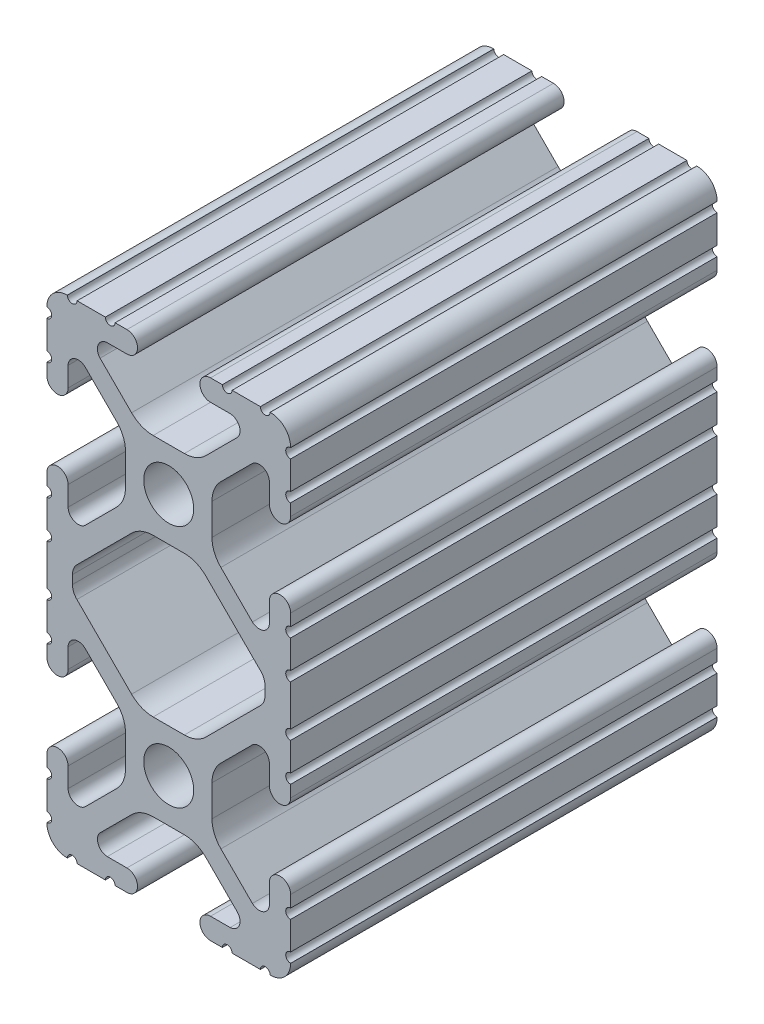
SolidWorks part; units mm, degrees
ref_plane "Front Plane" through (0, 0, 0) normal (0, 0, 1) x (1, 0, 0)
ref_plane "Top Plane" through (0, 0, 0) normal (0, 1, 0) x (1, 0, 0)
ref_plane "Right Plane" through (0, 0, 0) normal (1, 0, 0) x (0, 0, -1)
sketch "Sketch1" plane through (0, 0, 0) normal (0, 0, 1) x (1, 0, 0)
  line L0 (902.297, 599.2494) -> (902.297, 600.1524)
  line L1 (902.7583, 601.2659) -> (908.4588, 606.9666)
  line L2 (910.7039, 607.8966) -> (913.9563, 607.8966)
  line L3 (916.2014, 606.9666) -> (921.9018, 601.266)
  line L4 (922.363, 600.1525) -> (922.363, 599.2495)
  line L5 (921.9018, 598.136) -> (916.2013, 592.4353)
  line L6 (913.9562, 591.5053) -> (910.7038, 591.5053)
  line L7 (908.4587, 592.4353) -> (902.7583, 598.1358)
  line L8 (925.03, 602.8505) -> (925.03, 605.7969)
  line L9 (925.03, 606.8129) -> (925.03, 608.0448)
  line L10 (922.8202, 608.0448) -> (922.8202, 605.996)
  line L11 (921.0484, 605.2457) -> (917.7644, 608.5297)
  line L12 (916.8344, 610.7748) -> (916.8344, 614.0272)
  line L13 (917.7644, 616.2723) -> (921.0482, 619.556)
  line L14 (922.8202, 618.7995) -> (922.8202, 616.757)
  line L15 (925.03, 616.757) -> (925.03, 617.9889)
  line L16 (925.03, 619.0049) -> (925.03, 621.9513)
  line L17 (925.03, 622.9673) -> (925.03, 622.9927)
  line L18 (922.9218, 625.1009) -> (922.8964, 625.1009)
  line L19 (921.8804, 625.1009) -> (918.934, 625.1009)
  line L20 (917.918, 625.1009) -> (916.6861, 625.1009)
  line L21 (916.6861, 622.8911) -> (918.735, 622.8911)
  line L22 (919.4852, 621.1193) -> (916.2013, 617.8353)
  line L23 (913.9562, 616.9053) -> (910.7038, 616.9053)
  line L24 (908.4587, 617.8353) -> (905.175, 621.1191)
  line L25 (905.9315, 622.8911) -> (907.9739, 622.8911)
  line L26 (907.9739, 625.1009) -> (906.742, 625.1009)
  line L27 (905.726, 625.1009) -> (902.7796, 625.1009)
  line L28 (901.7636, 625.1009) -> (901.7382, 625.1009)
  line L29 (899.63, 622.9927) -> (899.63, 622.9673)
  line L30 (899.63, 621.9513) -> (899.63, 619.0049)
  line L31 (899.63, 617.9889) -> (899.63, 616.757)
  line L32 (901.8398, 616.757) -> (901.8398, 618.8059)
  line L33 (903.6117, 619.5561) -> (906.8957, 616.2722)
  line L34 (907.8257, 614.0271) -> (907.8257, 610.7747)
  line L35 (906.8957, 608.5296) -> (903.6119, 605.2459)
  line L36 (901.8398, 606.0024) -> (901.8398, 608.0448)
  line L37 (899.63, 608.0448) -> (899.63, 606.8129)
  line L38 (899.63, 605.7969) -> (899.63, 602.8505)
  line L39 (899.63, 601.8345) -> (899.63, 597.5673)
  line L40 (899.63, 596.5513) -> (899.63, 593.6049)
  line L41 (899.63, 592.5889) -> (899.63, 591.357)
  line L42 (901.8398, 591.357) -> (901.8398, 593.4059)
  line L43 (903.6117, 594.1561) -> (906.8957, 590.8722)
  line L44 (907.8257, 588.6271) -> (907.8257, 585.3747)
  line L45 (906.8957, 583.1296) -> (903.6119, 579.8459)
  line L46 (901.8398, 580.6024) -> (901.8398, 582.6448)
  line L47 (899.63, 582.6448) -> (899.63, 581.4129)
  line L48 (899.63, 580.3969) -> (899.63, 577.4505)
  line L49 (899.63, 576.4345) -> (899.63, 576.4091)
  line L50 (901.7382, 574.3009) -> (901.7636, 574.3009)
  line L51 (902.7796, 574.3009) -> (905.726, 574.3009)
  line L52 (906.742, 574.3009) -> (907.9739, 574.3009)
  line L53 (907.9739, 576.5107) -> (905.9251, 576.5107)
  line L54 (905.1749, 578.2826) -> (908.4588, 581.5666)
  line L55 (910.7039, 582.4966) -> (913.9563, 582.4966)
  line L56 (916.2014, 581.5666) -> (919.4851, 578.2828)
  line L57 (918.7286, 576.5107) -> (916.6861, 576.5107)
  line L58 (916.6861, 574.3009) -> (917.918, 574.3009)
  line L59 (918.934, 574.3009) -> (921.8804, 574.3009)
  line L60 (922.8964, 574.3009) -> (922.9218, 574.3009)
  line L61 (925.03, 576.4091) -> (925.03, 576.4345)
  line L62 (925.03, 577.4505) -> (925.03, 580.3969)
  line L63 (925.03, 581.4129) -> (925.03, 582.6448)
  line L64 (922.8202, 582.6448) -> (922.8202, 580.596)
  line L65 (921.0484, 579.8457) -> (917.7644, 583.1297)
  line L66 (916.8344, 585.3748) -> (916.8344, 588.6272)
  line L67 (917.7644, 590.8723) -> (921.0482, 594.156)
  line L68 (922.8202, 593.3995) -> (922.8202, 591.357)
  line L69 (925.03, 591.357) -> (925.03, 592.5889)
  line L70 (925.03, 593.6049) -> (925.03, 596.5513)
  line L71 (925.03, 597.5673) -> (925.03, 601.8345)
  arc A0 (902.7583, 601.2659) -> (902.297, 600.1524) centre (903.8718, 600.1524) ccw
  arc A1 (910.7039, 607.8966) -> (908.4588, 606.9666) centre (910.7039, 604.7216) ccw
  arc A2 (916.2014, 606.9666) -> (913.9563, 607.8966) centre (913.9563, 604.7216) ccw
  arc A3 (922.363, 600.1525) -> (921.9018, 601.266) centre (920.7882, 600.1525) ccw
  arc A4 (921.9018, 598.136) -> (922.363, 599.2495) centre (920.7882, 599.2495) ccw
  arc A5 (913.9562, 591.5053) -> (916.2013, 592.4353) centre (913.9562, 594.6803) ccw
  arc A6 (908.4587, 592.4353) -> (910.7038, 591.5053) centre (910.7038, 594.6803) ccw
  arc A7 (902.297, 599.2494) -> (902.7583, 598.1358) centre (903.8718, 599.2494) ccw
  circle A8 centre (912.33, 612.4009) radius 2.6035
  circle A9 centre (912.33, 587.0009) radius 2.6035
  arc A10 (925.03, 602.8505) -> (925.03, 601.8345) centre (925.03, 602.3425) ccw
  arc A11 (925.03, 606.8129) -> (925.03, 605.7969) centre (925.03, 606.3049) ccw
  arc A12 (925.03, 608.0448) -> (922.8202, 608.0448) centre (923.9251, 608.0448) ccw
  arc A13 (921.0484, 605.2457) -> (922.8202, 605.996) centre (921.7603, 606.0319) ccw
  arc A14 (916.8344, 610.7748) -> (917.7644, 608.5297) centre (920.0094, 610.7748) ccw
  arc A15 (917.7644, 616.2723) -> (916.8344, 614.0272) centre (920.0094, 614.0272) ccw
  arc A16 (922.8202, 618.7995) -> (921.0482, 619.556) centre (921.7601, 618.7699) ccw
  arc A17 (922.8202, 616.757) -> (925.03, 616.757) centre (923.9251, 616.757) ccw
  arc A18 (925.03, 619.0049) -> (925.03, 617.9889) centre (925.03, 618.4969) ccw
  arc A19 (925.03, 622.9673) -> (925.03, 621.9513) centre (925.03, 622.4593) ccw
  arc A20 (925.03, 622.9927) -> (922.9218, 625.1009) centre (922.9218, 622.9927) ccw
  arc A21 (921.8804, 625.1009) -> (922.8964, 625.1009) centre (922.3884, 625.1009) ccw
  arc A22 (917.918, 625.1009) -> (918.934, 625.1009) centre (918.426, 625.1009) ccw
  arc A23 (916.6861, 625.1009) -> (916.6861, 622.8911) centre (916.6861, 623.996) ccw
  arc A24 (919.4852, 621.1193) -> (918.735, 622.8911) centre (918.6991, 621.8312) ccw
  arc A25 (913.9562, 616.9053) -> (916.2013, 617.8353) centre (913.9562, 620.0803) ccw
  arc A26 (908.4587, 617.8353) -> (910.7038, 616.9053) centre (910.7038, 620.0803) ccw
  arc A27 (905.9315, 622.8911) -> (905.175, 621.1191) centre (905.9611, 621.831) ccw
  arc A28 (907.9739, 622.8911) -> (907.9739, 625.1009) centre (907.9739, 623.996) ccw
  arc A29 (905.726, 625.1009) -> (906.742, 625.1009) centre (906.234, 625.1009) ccw
  arc A30 (901.7636, 625.1009) -> (902.7796, 625.1009) centre (902.2716, 625.1009) ccw
  arc A31 (901.7382, 625.1009) -> (899.63, 622.9927) centre (901.7382, 622.9927) ccw
  arc A32 (899.63, 621.9513) -> (899.63, 622.9673) centre (899.63, 622.4593) ccw
  arc A33 (899.63, 617.9889) -> (899.63, 619.0049) centre (899.63, 618.4969) ccw
  arc A34 (899.63, 616.757) -> (901.8398, 616.757) centre (900.7349, 616.757) ccw
  arc A35 (903.6117, 619.5561) -> (901.8398, 618.8059) centre (902.8998, 618.77) ccw
  arc A36 (907.8257, 614.0271) -> (906.8957, 616.2722) centre (904.6507, 614.0271) ccw
  arc A37 (906.8957, 608.5296) -> (907.8257, 610.7747) centre (904.6507, 610.7747) ccw
  arc A38 (901.8398, 606.0024) -> (903.6119, 605.2459) centre (902.9, 606.032) ccw
  arc A39 (901.8398, 608.0448) -> (899.63, 608.0448) centre (900.7349, 608.0448) ccw
  arc A40 (899.63, 605.7969) -> (899.63, 606.8129) centre (899.63, 606.3049) ccw
  arc A41 (899.63, 601.8345) -> (899.63, 602.8505) centre (899.63, 602.3425) ccw
  arc A42 (899.63, 596.5513) -> (899.63, 597.5673) centre (899.63, 597.0593) ccw
  arc A43 (899.63, 592.5889) -> (899.63, 593.6049) centre (899.63, 593.0969) ccw
  arc A44 (899.63, 591.357) -> (901.8398, 591.357) centre (900.7349, 591.357) ccw
  arc A45 (903.6117, 594.1561) -> (901.8398, 593.4059) centre (902.8998, 593.37) ccw
  arc A46 (907.8257, 588.6271) -> (906.8957, 590.8722) centre (904.6507, 588.6271) ccw
  arc A47 (906.8957, 583.1296) -> (907.8257, 585.3747) centre (904.6507, 585.3747) ccw
  arc A48 (901.8398, 580.6024) -> (903.6119, 579.8459) centre (902.9, 580.632) ccw
  arc A49 (901.8398, 582.6448) -> (899.63, 582.6448) centre (900.7349, 582.6448) ccw
  arc A50 (899.63, 580.3969) -> (899.63, 581.4129) centre (899.63, 580.9049) ccw
  arc A51 (899.63, 576.4345) -> (899.63, 577.4505) centre (899.63, 576.9425) ccw
  arc A52 (899.63, 576.4091) -> (901.7382, 574.3009) centre (901.7382, 576.4091) ccw
  arc A53 (902.7796, 574.3009) -> (901.7636, 574.3009) centre (902.2716, 574.3009) ccw
  arc A54 (906.742, 574.3009) -> (905.726, 574.3009) centre (906.234, 574.3009) ccw
  arc A55 (907.9739, 574.3009) -> (907.9739, 576.5107) centre (907.9739, 575.4058) ccw
  arc A56 (905.1749, 578.2826) -> (905.9251, 576.5107) centre (905.961, 577.5707) ccw
  arc A57 (910.7039, 582.4966) -> (908.4588, 581.5666) centre (910.7039, 579.3216) ccw
  arc A58 (916.2014, 581.5666) -> (913.9563, 582.4966) centre (913.9563, 579.3216) ccw
  arc A59 (918.7286, 576.5107) -> (919.4851, 578.2828) centre (918.699, 577.5709) ccw
  arc A60 (916.6861, 576.5107) -> (916.6861, 574.3009) centre (916.6861, 575.4058) ccw
  arc A61 (918.934, 574.3009) -> (917.918, 574.3009) centre (918.426, 574.3009) ccw
  arc A62 (922.8964, 574.3009) -> (921.8804, 574.3009) centre (922.3884, 574.3009) ccw
  arc A63 (922.9218, 574.3009) -> (925.03, 576.4091) centre (922.9218, 576.4091) ccw
  arc A64 (925.03, 577.4505) -> (925.03, 576.4345) centre (925.03, 576.9425) ccw
  arc A65 (925.03, 581.4129) -> (925.03, 580.3969) centre (925.03, 580.9049) ccw
  arc A66 (925.03, 582.6448) -> (922.8202, 582.6448) centre (923.9251, 582.6448) ccw
  arc A67 (921.0484, 579.8457) -> (922.8202, 580.596) centre (921.7603, 580.6319) ccw
  arc A68 (916.8344, 585.3748) -> (917.7644, 583.1297) centre (920.0094, 585.3748) ccw
  arc A69 (917.7644, 590.8723) -> (916.8344, 588.6272) centre (920.0094, 588.6272) ccw
  arc A70 (922.8202, 593.3995) -> (921.0482, 594.156) centre (921.7601, 593.3699) ccw
  arc A71 (922.8202, 591.357) -> (925.03, 591.357) centre (923.9251, 591.357) ccw
  arc A72 (925.03, 593.6049) -> (925.03, 592.5889) centre (925.03, 593.0969) ccw
  arc A73 (925.03, 597.5673) -> (925.03, 596.5513) centre (925.03, 597.0593) ccw
extrude "Extrude1" add sketch "Sketch1" against normal blind 44.45
